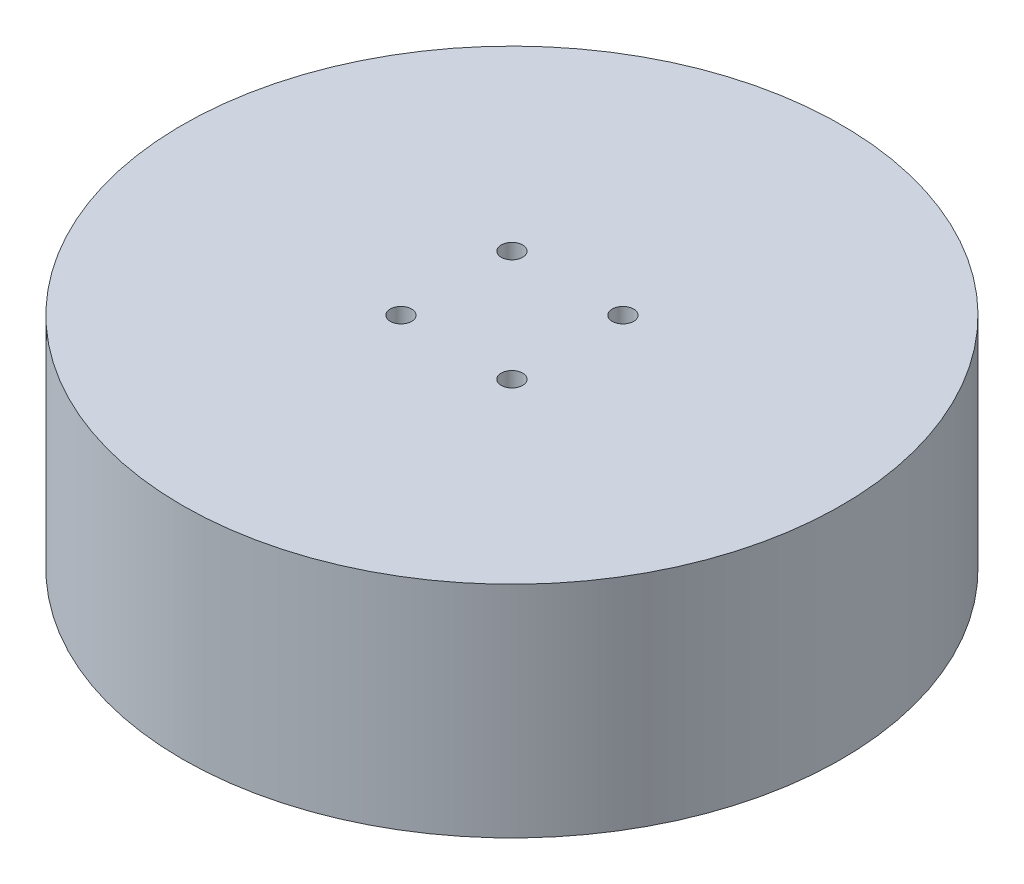
SolidWorks part; units mm, degrees
ref_plane "Front Plane" through (0, 0, 0) normal (0, 0, 1) x (1, 0, 0)
ref_plane "Top Plane" through (0, 0, 0) normal (0, 1, 0) x (1, 0, 0)
ref_plane "Right Plane" through (0, 0, 0) normal (1, 0, 0) x (0, 0, -1)
sketch "Sketch1" plane through (0, 0, 0) normal (0, 1, 0) x (1, 0, 0)
  circle A0 centre (0, 0) radius 31.5
extrude "Boss-Extrude1" add sketch "Sketch1" along normal blind 21
hole_wizard "Tap Drill for M2.5x0.45 Tap2" positions "Sketch5" profile "Sketch4" hole size "M2.5x0.45" standard "ANSI Metric"
sketch "Sketch5" plane through (0, 21, 0) normal (0, 1, 0) x (1, 0, 0)
  line L2 (0, 0) -> (-5.3033, 5.3033) construction
  line L4 (0, 0) -> (5.3033, 5.3033) construction
  line L7 (5.3033, -5.3033) -> (0, 0) construction
  line L8 (0, 0) -> (-5.3033, -5.3033) construction
  point P40 (-5.3033, 5.3033)
  point P46 (5.3033, 5.3033)
  point P51 (5.3033, -5.3033)
  point P55 (-5.3033, -5.3033)
sketch "Sketch4" plane through (-5.3033, 21, -5.3033) normal (1, 0, 0) x (0, 0, 1)
  line L0 (0, 0) -> (0, 7.6159)
  line L1 (0, 7.6159) -> (1.025, 7)
  line L2 (1.025, 7) -> (1.025, 0)
  line L5 (1.025, 0) -> (0, 0)
  line L10 (0, 7.6159) -> (-1.025, 7) construction
  line L11 (0, -6.35) -> (0, 107.95) construction
  dimension "Hole Dia." = 2.05
  dimension "Hole Depth" = 7
  dimension "Drill Angle" = 118
sketch "Sketch6" plane through (0, 0, 0) normal (0, -1, 0) x (1, 0, 0)
  circle A0 centre (0, 0) radius 27
extrude "Cut-Extrude1" cut sketch "Sketch6" against normal blind 10
